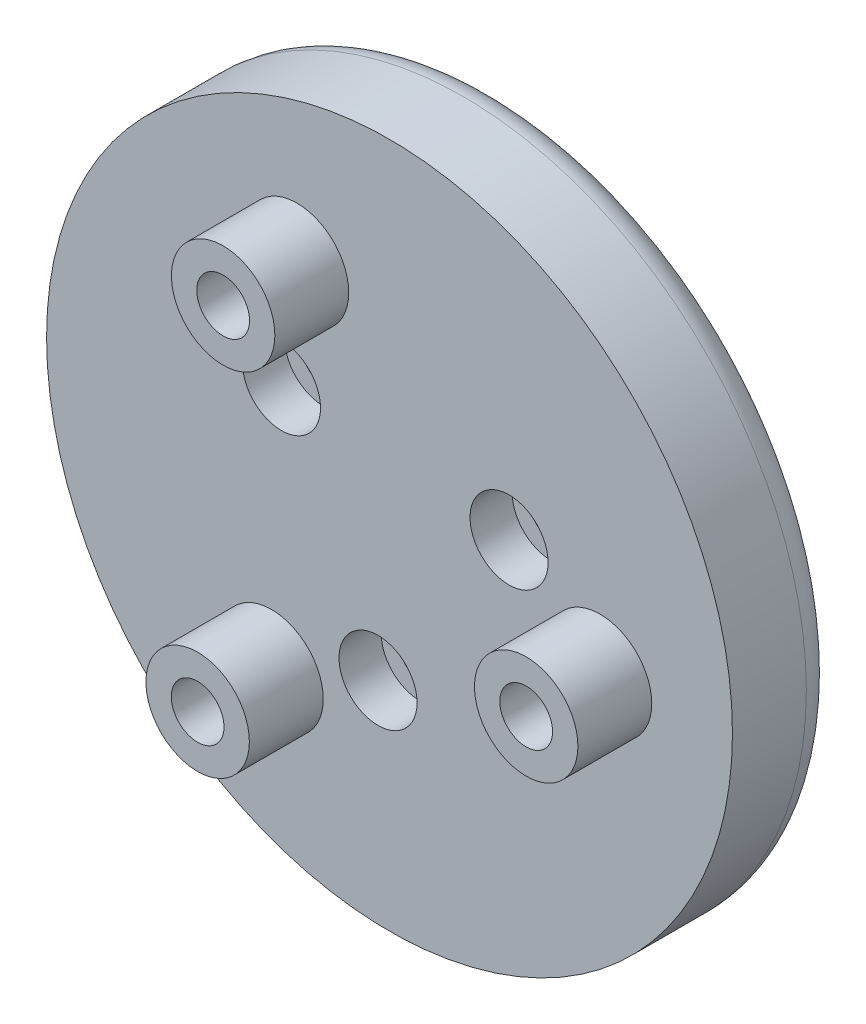
SolidWorks part; units mm, degrees
ref_plane "Front Plane" through (0, 0, 0) normal (0, 0, 1) x (1, 0, 0)
ref_plane "Top Plane" through (0, 0, 0) normal (0, 1, 0) x (1, 0, 0)
ref_plane "Right Plane" through (0, 0, 0) normal (1, 0, 0) x (0, 0, -1)
sketch "Sketch1" plane through (0, 0, 0) normal (0, 0, 1) x (1, 0, 0)
  line L0 (0, 0) -> (0, -26.3138) construction
  line L1 (0, 0) -> (-1.4163, -16.1882) construction
  line L2 (0, 0) -> (-5.1197, 3.5849) construction
  line L3 (0, 0) -> (5.6644, 2.6414) construction
  line L4 (0, 0) -> (-9.0869, -13.4719) construction
  line L5 (0, 0) -> (-7.1235, 14.6054) construction
  line L6 (0, 0) -> (16.2104, -1.1335) construction
  line L7 (0, 0) -> (-40.5768, 0) construction
  circle A0 centre (0, 0) radius 16.25
  circle A1 centre (0, 0) radius 6.25 construction
  circle A2 centre (-0.5447, -6.2262) radius 1
  circle A3 centre (-5.1197, 3.5849) radius 1
  circle A4 centre (5.6644, 2.6414) radius 1
  circle A5 centre (0, 0) radius 10 construction
  circle A6 centre (-5.5919, -8.2904) radius 1.25
  circle A7 centre (-4.3837, 8.9879) radius 1.25
  circle A8 centre (9.9756, -0.6976) radius 1.25
  dimension "D1" = 32.5
  dimension "D2" = 12.5
  dimension "D4" = 2
  dimension "D7" = 2
  dimension "D8" = 2
  dimension "D9" = 20
  dimension "D11" = 2.5
  dimension "D12" = 2.5
  dimension "D13" = 2.5
  dimension "D3" = 5
  dimension "D5" = 120
  dimension "D6" = 120
  dimension "D10" = 34
  dimension "D14" = 120
  dimension "D15" = 120
extrude "Boss-Extrude1" add sketch "Sketch1" along normal blind 5
fillet "Fillet1" radius 1.5 1 edges at (16.25, 0, 0)
sketch "Sketch2" plane through (0, 0, 5) normal (0, 0, 1) x (1, 0, 0)
  circle A0 centre (-5.5919, -8.2904) radius 2.45
  circle A1 centre (-4.3837, 8.9879) radius 2.45
  circle A2 centre (9.9756, -0.6976) radius 2.45
  dimension "D1" = 4.9
  dimension "D2" = 4.9
  dimension "D3" = 4.9
extrude "Boss-Extrude2" add sketch "Sketch2" along normal blind 3.5
sketch "Sketch4" plane through (0, 0, 0) normal (0, 0, -1) x (-1, 0, 0)
  circle A0 centre (4.3837, 8.9879) radius 1.25
  circle A1 centre (-9.9756, -0.6976) radius 1.25
  circle A2 centre (5.5919, -8.2904) radius 1.25
  circle A3 centre (-9.9756, -0.6976) radius 1.25 construction
  circle A4 centre (4.3837, 8.9879) radius 1.25 construction
  circle A5 centre (5.5919, -8.2904) radius 1.25 construction
extrude "Cut-Extrude1" cut sketch "Sketch4" against normal through all both and the other way through all
sketch "Sketch5" plane through (0, 0, 5) normal (0, 0, 1) x (1, 0, 0)
  circle A0 centre (5.6644, 2.6414) radius 1.85
  circle A1 centre (-5.1197, 3.5849) radius 1.85
  circle A2 centre (-0.5447, -6.2262) radius 1.85
  dimension "D1" = 3.7
  dimension "D2" = 3.7
  dimension "D3" = 3.7
extrude "Cut-Extrude2" cut sketch "Sketch5" against normal blind 2
